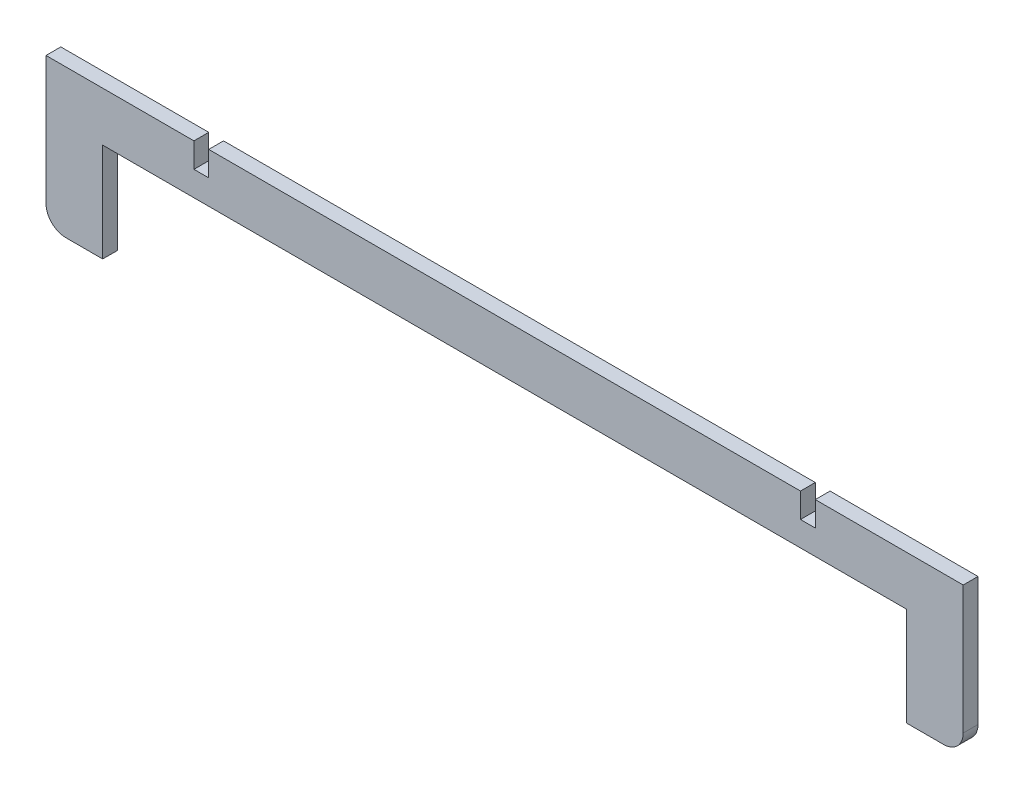
SolidWorks part; units mm, degrees
ref_plane "Front Plane" through (0, 0, 0) normal (0, 0, 1) x (1, 0, 0)
ref_plane "Top Plane" through (0, 0, 0) normal (0, 1, 0) x (1, 0, 0)
ref_plane "Right Plane" through (0, 0, 0) normal (1, 0, 0) x (0, 0, -1)
sketch "Sketch1" plane through (0, 0, 0) normal (0, 0, 1) x (1, 0, 0)
  line L1 (-93, 15) -> (-63, 15)
  line L2 (-93, 15) -> (-93, -15)
  line L3 (-93, -15) -> (93, -15)
  line L4 (93, 15) -> (93, -15)
  line L5 (-93, 15) -> (93, -15) construction
  line L6 (-93, -15) -> (93, 15) construction
  line L7 (-60, 15) -> (60, 15)
  line L9 (-60, 10) -> (-60, 15)
  line L11 (-63, 10) -> (-63, 15)
  line L13 (60, 10) -> (60, 15)
  line L15 (63, 10) -> (63, 15)
  line L16 (63, 15) -> (93, 15)
  line L17 (-60, 10) -> (-63, 10)
  line L18 (60, 10) -> (63, 10)
  point P0 (0, 0)
  point P12 (-61.5, 10)
  dimension "D1" = 60
  dimension "D2" = 30
  dimension "D3" = 186
  dimension "D4" = 5
  dimension "D5" = 120
  dimension "D6" = 5
extrude "Boss-Extrude1" add sketch "Sketch1" along normal blind 3
sketch "Sketch2" plane through (0, 0, 3) normal (0, 0, 1) x (1, 0, 0)
  line L0 (-93, -15) -> (93, -15) construction
  line L1 (-81.5, 5) -> (81.5, 5)
  line L2 (-81.5, 5) -> (-81.5, -35)
  line L3 (-81.5, -35) -> (81.5, -35)
  line L4 (81.5, 5) -> (81.5, -35)
  line L5 (-81.5, 5) -> (81.5, -35) construction
  line L6 (-81.5, -35) -> (81.5, 5) construction
  point P0 (0, -15)
  dimension "D1" = 40
  dimension "D2" = 163
extrude "Cut-Extrude1" cut sketch "Sketch2" against normal blind 3
fillet "Fillet1" radius 4 2 edges at (93, -15, 1.5) (-93, -15, 1.5)
